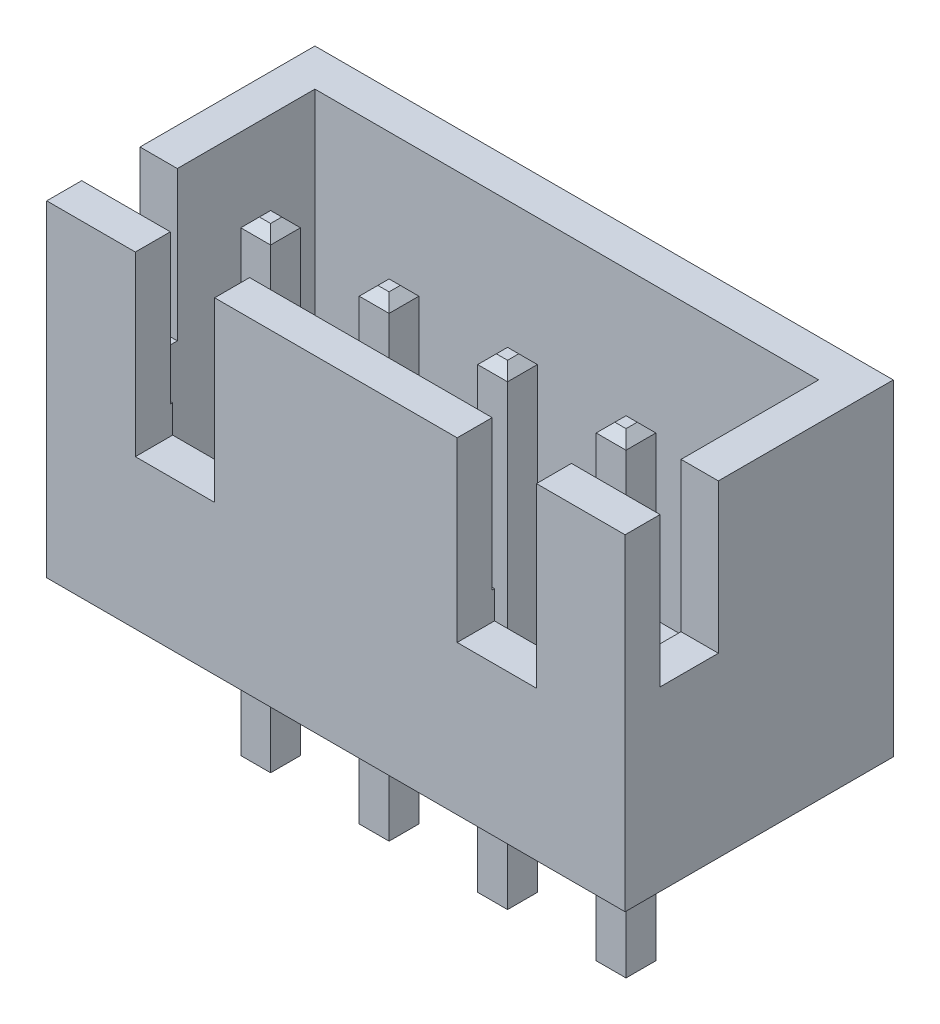
SolidWorks part; units mm, degrees
other "Camera1"
ref_plane "Front Plane" through (0, 0, 0) normal (0, 0, 1) x (1, 0, 0)
ref_plane "Top Plane" through (0, 0, 0) normal (0, 1, 0) x (1, 0, 0)
ref_plane "Right Plane" through (0, 0, 0) normal (1, 0, 0) x (0, 0, -1)
sketch "Sketch1" plane through (0, 0, 0) normal (0, 1, 0) x (1, 0, 0)
  line L1 (-6.2, 2.875) -> (6.2, 2.875)
  line L2 (-6.2, 2.875) -> (-6.2, -2.875)
  line L3 (-6.2, -2.875) -> (6.2, -2.875)
  line L4 (6.2, 2.875) -> (6.2, -2.875)
  line L5 (-6.2, 2.875) -> (6.2, -2.875) construction
  line L6 (-6.2, -2.875) -> (6.2, 2.875) construction
  point P0 (0, 0)
  dimension "D1" = 5.75
  dimension "D2" = 12.4
extrude "Boss-Extrude1" add sketch "Sketch1" along normal blind 7
shell "Shell1" thickness 0.8
sketch "Sketch2" plane through (6.2, 0, 0) normal (1, 0, 0) x (0, 0, -1)
  line L0 (-0.875, 7) -> (-0.875, 3.8)
  line L1 (-2.875, 7) -> (2.875, 7) construction
  line L2 (-2.125, 3.8) -> (-2.125, 7)
  line L3 (-2.125, 7) -> (-0.875, 7)
  line L4 (-2.875, 7) -> (-2.875, 0) construction
  line L5 (-0.875, 3.8) -> (-2.125, 3.8)
  dimension "D1" = 0.75
  dimension "D2" = 1.25
  dimension "D3" = 3.2
extrude "Cut-Extrude1" cut sketch "Sketch2" against normal through all
sketch "Sketch3" plane through (0, 0, 2.875) normal (0, 0, 1) x (1, 0, 0)
  line L0 (-4.3, 7) -> (-4.3, 3.2)
  line L1 (-6.2, 7) -> (6.2, 7) construction
  line L2 (-6.2, 7) -> (-6.2, 0) construction
  line L3 (-2.6, 3.2) -> (-4.3, 3.2)
  line L4 (4.3, 3.2) -> (2.6, 3.2)
  line L5 (-2.6, 3.2) -> (-2.6, 7)
  line L6 (-2.6, 7) -> (-4.3, 7)
  line L8 (0, 7) -> (0, 0) construction
  line L9 (2.6, 7) -> (4.3, 7)
  line L10 (2.6, 3.2) -> (2.6, 7)
  line L14 (4.3, 7) -> (4.3, 3.2)
  dimension "D1" = 1.9
  dimension "D2" = 1.7
  dimension "D3" = 3.8
extrude "Cut-Extrude2" cut sketch "Sketch3" against normal up to next
sketch "Sketch4" plane through (0, 0, 0) normal (0, -1, 0) x (1, 0, 0)
  line L0 (-6.2, -2.875) -> (-6.2, 2.875) construction
  line L1 (-4.07, 0.845) -> (-3.43, 0.845)
  line L2 (-4.07, 0.845) -> (-4.07, 0.205)
  line L3 (-4.07, 0.205) -> (-3.43, 0.205)
  line L4 (-3.43, 0.845) -> (-3.43, 0.205)
  line L5 (-4.07, 0.845) -> (-3.43, 0.205) construction
  line L6 (-4.07, 0.205) -> (-3.43, 0.845) construction
  line L9 (-6.2, 2.875) -> (6.2, 2.875) construction
  line L10 (-1.53, 0.845) -> (-0.89, 0.845)
  line L11 (-0.89, 0.845) -> (-0.89, 0.205)
  line L12 (-1.53, 0.205) -> (-0.89, 0.205)
  line L13 (-1.53, 0.845) -> (-1.53, 0.205)
  line L14 (1.01, 0.845) -> (1.65, 0.845)
  line L15 (1.65, 0.845) -> (1.65, 0.205)
  line L16 (1.01, 0.205) -> (1.65, 0.205)
  line L17 (1.01, 0.845) -> (1.01, 0.205)
  line L18 (3.55, 0.845) -> (4.19, 0.845)
  line L19 (4.19, 0.845) -> (4.19, 0.205)
  line L20 (3.55, 0.205) -> (4.19, 0.205)
  line L21 (3.55, 0.845) -> (3.55, 0.205)
  point P0 (-3.75, 0.525)
  dimension "D1" = 0.64
  dimension "D2" = 0.64
  dimension "D3" = 2.45
  dimension "D4" = 2.35
  dimension "D5" = 4
extrude "Boss-Extrude2" add sketch "Sketch4" along normal blind 3.45 and the other way blind 6.75
chamfer "Chamfer1" distance 0.2 angle 45 32 edges at (3.55, -3.45, 0.525) (3.87, -3.45, 0.845) (4.19, -3.45, 0.525) (3.87, -3.45, 0.205) (1.01, -3.45, 0.525) (1.33, -3.45, 0.845) (1.65, -3.45, 0.525) (1.33, -3.45, 0.205) (-1.53, -3.45, 0.525) (-1.21, -3.45, 0.845) (-0.89, -3.45, 0.525) (-1.21, -3.45, 0.205) (-3.75, -3.45, 0.205) (-4.07, -3.45, 0.525) (-3.75, -3.45, 0.845) (-3.43, -3.45, 0.525) (4.19, 6.75, 0.525) (3.87, 6.75, 0.845) (3.55, 6.75, 0.525) (3.87, 6.75, 0.205) (1.65, 6.75, 0.525) (1.33, 6.75, 0.845) (1.01, 6.75, 0.525) (1.33, 6.75, 0.205) (-0.89, 6.75, 0.525) (-1.21, 6.75, 0.845) (-1.53, 6.75, 0.525) (-1.21, 6.75, 0.205) (-3.75, 6.75, 0.845) (-4.07, 6.75, 0.525) (-3.75, 6.75, 0.205) (-3.43, 6.75, 0.525)
